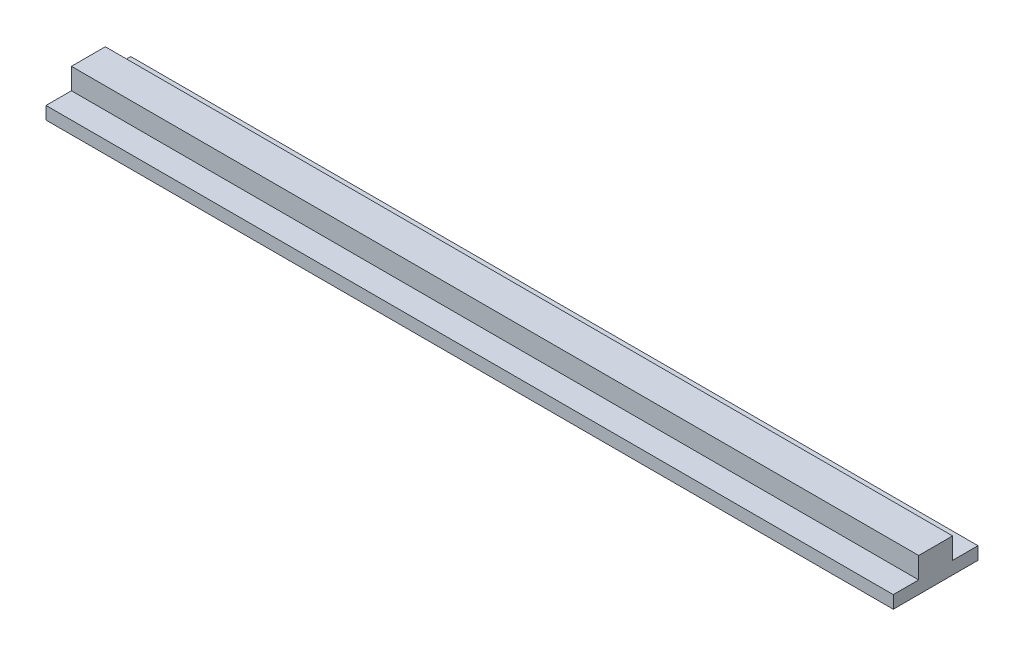
SolidWorks part; units mm, degrees
ref_plane "Plano frontal" through (0, 0, 0) normal (0, 0, 1) x (1, 0, 0)
ref_plane "Plano superior" through (0, 0, 0) normal (0, 1, 0) x (1, 0, 0)
ref_plane "Plano direito" through (0, 0, 0) normal (1, 0, 0) x (0, 0, -1)
sketch "Esboço1" plane through (0, 0, 0) normal (1, 0, 0) x (0, 0, -1)
  line L0 (0, 0) -> (0, 237.8173) construction
  line L1 (0, 0) -> (319.0578, 0) construction
  line L2 (-40, 80) -> (40, 80)
  line L3 (40, 80) -> (40, 30)
  line L4 (40, 30) -> (100, 30)
  line L5 (100, 30) -> (100, 0)
  line L6 (100, 0) -> (-100, 0)
  line L7 (-40, 80) -> (-40, 30)
  line L8 (-100, 30) -> (-100, 0)
  line L9 (-40, 30) -> (-100, 30)
  point P10 (0, 80)
  dimension "D1" = 80
  dimension "D2" = 50
  dimension "D3" = 30
  dimension "D4" = 200
extrude "Ressalto-extrusão1" add sketch "Esboço1" along normal mid plane 2000
sketch "Esboço2" plane through (0, 0, 0) normal (0, -1, 0) x (-1, 0, 0)
  circle A0 centre (0, 0) radius 20
  dimension "D1" = 40
extrude "Ressalto-extrusão2" add sketch "Esboço2" along normal blind 30
